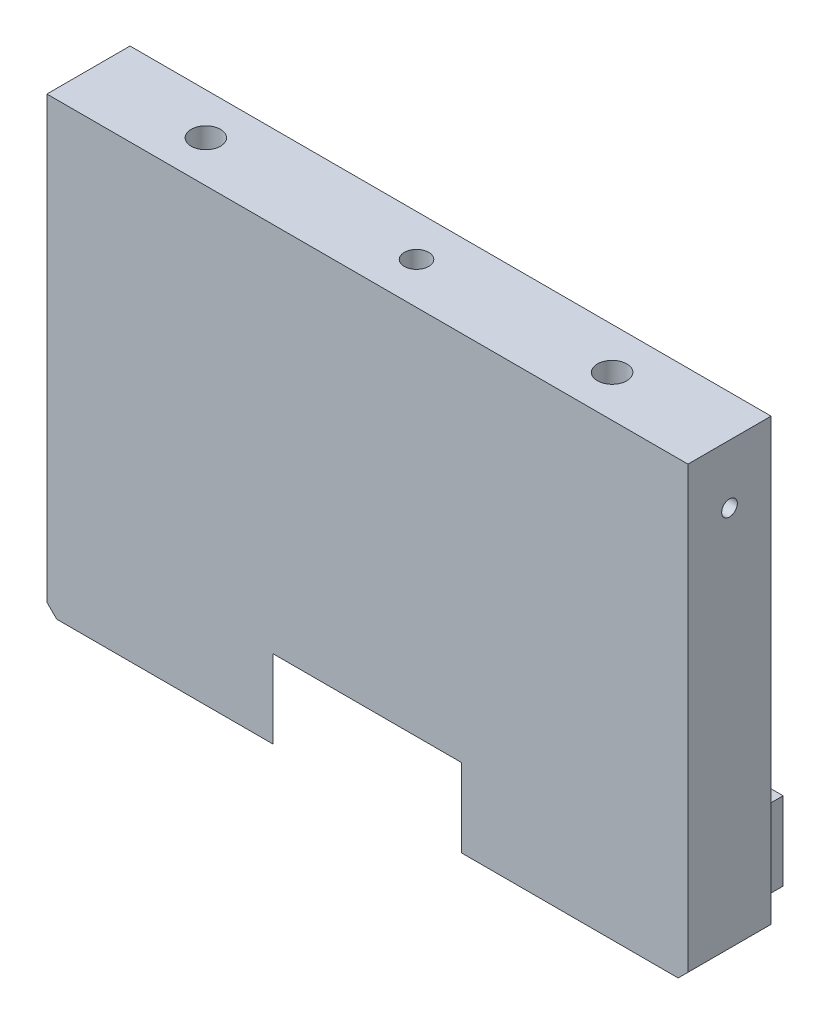
SolidWorks part; units mm, degrees
material "6061-T6 (SS)"
ref_plane "Front" through (0, 0, 0) normal (0, 0, 1) x (1, 0, 0)
ref_plane "Top" through (0, 0, 0) normal (0, 1, 0) x (1, 0, 0)
ref_plane "Right" through (0, 0, 0) normal (1, 0, 0) x (0, 0, -1)
sketch "Sketch1" plane through (0, 0, 0) normal (0, 0, 1) x (1, 0, 0)
  line L1 (-32.77, 23) -> (32.77, 23)
  line L2 (-32.77, 23) -> (-32.77, -23)
  line L3 (-32.77, -23) -> (32.77, -23)
  line L4 (32.77, 23) -> (32.77, -23)
  line L5 (-32.77, 23) -> (32.77, -23) construction
  line L6 (-32.77, -23) -> (32.77, 23) construction
  point P0 (0, 0)
  dimension "D1" = 65.54
  dimension "D2" = 46
extrude "Boss-Extrude1" add sketch "Sketch1" along normal blind 3.5
sketch "Sketch2" plane through (0, 0, 0) normal (0, 0, -1) x (-1, 0, 0)
  line L0 (-29, -23) -> (-29, -15) construction
  line L1 (-29, -23) -> (29, -23)
  line L2 (-29, -23) -> (-29, -15)
  line L3 (-29, -15) -> (29, -15)
  line L4 (29, -23) -> (29, -15)
  line L5 (32.77, -23) -> (-32.77, -23) construction
  line L6 (29, -23) -> (29, -15) construction
  dimension "D1" = 8
extrude "Boss-Extrude2" add sketch "Sketch2" along normal blind 10
sketch "Sketch5" plane through (0, -23, 0) normal (0, -1, 0) x (1, 0, 0)
  line L7 (-26.3112, -10.5) -> (26.3112, -10.5)
  line L8 (9.4195, 4) -> (9.4195, 3.5704)
  line L9 (-9.6229, 4) -> (9.4195, 4)
  line L10 (-9.6229, 4) -> (-9.6229, 3.5023)
  arc A0 (-9.6229, 3.5023) -> (-26.3112, -10.5) centre (0, -24.9125) ccw
  arc A3 (26.3112, -10.5) -> (9.4195, 3.5704) centre (0, -24.9125) ccw
extrude "Cut-Extrude1" cut sketch "Sketch5" against normal blind 8
sketch "Sketch6" plane through (0, 0, 0) normal (0, 0, -1) x (-1, 0, 0)
  line L0 (-32.77, 23) -> (-32.77, -23)
  line L1 (-32.77, -23) -> (-29, -23)
  line L2 (-29, -23) -> (-29, -15)
  line L3 (-29, -15) -> (29, -15)
  line L4 (29, -15) -> (29, -23)
  line L5 (29, -23) -> (32.77, -23)
  line L6 (32.77, -23) -> (32.77, 23)
  line L7 (32.77, 23) -> (-32.77, 23)
extrude "Boss-Extrude3" add sketch "Sketch6" along normal blind 5
chamfer "Chamfer1" distance 1 angle 45 2 edges at (-32.77, -23, -0.75) (32.77, -23, -0.75)
hole_wizard "Ø3.0mm Dowel Hole1" positions "Sketch7" profile "Sketch8" hole size "Ø3.0" standard "ANSI Metric"
sketch "Sketch7" plane through (0, 23, 0) normal (0, 1, 0) x (1, 0, 0)
  line L0 (32.77, -3.5) -> (-32.77, -3.5) construction
  line L1 (-32.77, -3.5) -> (-32.77, 5) construction
  line L2 (32.77, -3.5) -> (32.77, 5) construction
  point P0 (-20.77, 0.75)
  point P2 (20.77, 0.75)
  dimension "D1" = 4.25
  dimension "D2" = 12
  dimension "D3" = 12
sketch "Sketch8" plane through (-20.77, 23, -0.75) normal (1, 0, 0) x (0, 0, 1)
  line L0 (0, 0) -> (0, 5.4013)
  line L1 (0, 5.4013) -> (1.5, 4.5)
  line L2 (1.5, 4.5) -> (1.5, 0)
  line L5 (1.5, 0) -> (0, 0)
  line L10 (0, 5.4013) -> (-1.5, 4.5) construction
  line L11 (0, -6.35) -> (0, 107.95) construction
  dimension "Hole Dia." = 3
  dimension "Hole Depth" = 4.5
  dimension "Drill Angle" = 118
hole_wizard "M3x0.5 Tapped Hole1" positions "Sketch9" profile "Sketch10" tap size "M3x0.5" standard "ANSI Metric"
sketch "Sketch9" plane through (0, 23, 0) normal (0, 1, 0) x (1, 0, 0)
  line L0 (32.77, -3.5) -> (-32.77, -3.5) construction
  line L1 (32.77, -3.5) -> (32.77, 5) construction
  point P0 (0.77, 0.75)
  dimension "D1" = 4.25
  dimension "D2" = 32
sketch "Sketch10" plane through (0.77, 23, -0.75) normal (1, 0, 0) x (0, 0, 1)
  line L0 (0, 0) -> (0, 8.2511)
  line L1 (0, 8.2511) -> (1.25, 7.5)
  line L2 (1.25, 7.5) -> (1.25, 0)
  line L5 (1.25, 0) -> (0, 0)
  line L10 (0, 8.2511) -> (-1.25, 7.5) construction
  line L11 (0, -6.35) -> (0, 107.95) construction
  dimension "Tap Drill Dia." = 2.5
  dimension "Tap Drill Depth" = 7.5
  dimension "Drill Angle" = 118
cosmetic thread "Hole Thread1" parameters "D1"=6, "D2"=3
hole_wizard "M2x0.4 Tapped Hole1" positions "Sketch11" profile "Sketch12" tap size "M2x0.4" standard "ANSI Metric"
sketch "Sketch11" plane through (0, -23, 0) normal (0, -1, 0) x (-1, 0, 0)
  point P0 (28.0334, 0.5)
sketch "Sketch12" plane through (-28.0334, -23, -0.5) normal (1, 0, 0) x (0, 0, -1)
  line L0 (0, 0) -> (0, 5.6807)
  line L1 (0, 5.6807) -> (0.8, 5.2)
  line L2 (0.8, 5.2) -> (0.8, 0)
  line L5 (0.8, 0) -> (0, 0)
  line L10 (0, 5.6807) -> (-0.8, 5.2) construction
  line L11 (0, -6.35) -> (0, 107.95) construction
  dimension "Tap Drill Dia." = 1.6
  dimension "Tap Drill Depth" = 5.2
  dimension "Drill Angle" = 118
cosmetic thread "Hole Thread2" parameters "D1"=4, "D2"=2
hole_wizard "M2x0.4 Tapped Hole2" positions "Sketch13" profile "Sketch14" tap size "M2x0.4" standard "ANSI Metric"
sketch "Sketch13" plane through (32.77, 0, 0) normal (1, 0, 0) x (0, 0, -1)
  point P0 (0.75, 17)
sketch "Sketch14" plane through (32.77, 17, -0.75) normal (0, 1, 0) x (0, 0, -1)
  line L0 (0, 0) -> (0, 5.6807)
  line L1 (0, 5.6807) -> (0.8, 5.2)
  line L2 (0.8, 5.2) -> (0.8, 0)
  line L5 (0.8, 0) -> (0, 0)
  line L10 (0, 5.6807) -> (-0.8, 5.2) construction
  line L11 (0, -6.35) -> (0, 107.95) construction
  dimension "Tap Drill Dia." = 1.6
  dimension "Tap Drill Depth" = 5.2
  dimension "Drill Angle" = 118
cosmetic thread "Hole Thread3" parameters "D1"=4, "D2"=2
